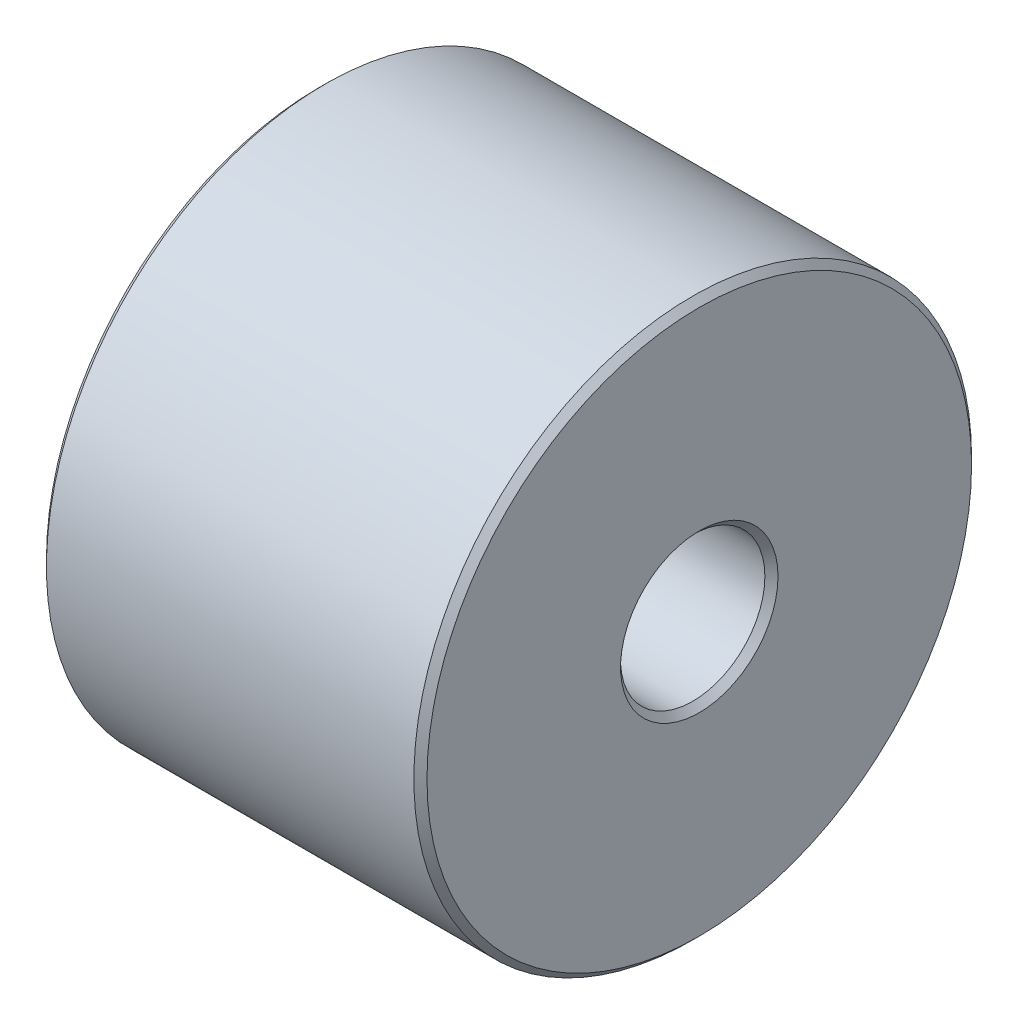
SolidWorks part; units mm, degrees
ref_plane "前视基准面" through (0, 0, 0) normal (0, 0, 1) x (1, 0, 0)
ref_plane "上视基准面" through (0, 0, 0) normal (0, 1, 0) x (1, 0, 0)
ref_plane "右视基准面" through (0, 0, 0) normal (1, 0, 0) x (0, 0, -1)
sketch "草图1" plane through (0, 0, 0) normal (1, 0, 0) x (0, 0, -1)
  circle A0 centre (0, 0) radius 8.5
  circle A1 centre (0, 0) radius 2.2
  dimension "D1" = 17
  dimension "D2" = 4.4
extrude "凸台-拉伸1" add sketch "草图1" along normal blind 11.6
chamfer "倒角1" distance 0.2 angle 45 4 edges at (11.6, 0, -8.5) (0, 0, -8.5) (11.6, 0, -2.2) (0, 0, -2.2)
